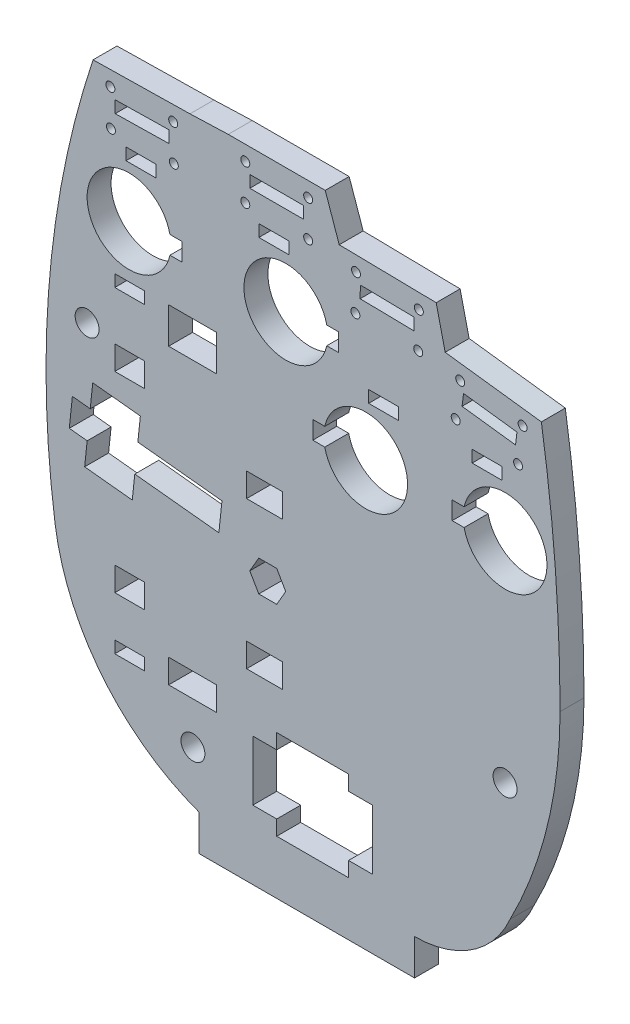
SolidWorks part; units mm, degrees
ref_plane "Front Plane" through (0, 0, 0) normal (0, 0, 1) x (1, 0, 0)
ref_plane "Top Plane" through (0, 0, 0) normal (0, 1, 0) x (1, 0, 0)
ref_plane "Right Plane" through (0, 0, 0) normal (1, 0, 0) x (0, 0, -1)
sketch "Sketch1" plane through (0, 0, 0) normal (0, 0, 1) x (1, 0, 0)
  line L0 (-4.5, 78.51) -> (-4.5, 76.51)
  line L1 (4.5, 78.51) -> (-4.5, 78.51)
  line L2 (-12.9786, -18) -> (-12.9786, -24)
  line L3 (-9.666, 24.0723) -> (-9.153, 28.9531)
  line L4 (-4.5, 76.51) -> (4.5, 76.51)
  line L5 (4.5, 76.51) -> (4.5, 78.51)
  line L6 (-34.6568, 26.6989) -> (-34.1438, 31.5798)
  line L7 (10.3588, 63.1512) -> (10.3588, 60.1512)
  line L8 (-8.1, 82.51) -> (8.1, 82.51)
  line L9 (8.3588, 63.1512) -> (10.3588, 63.1512)
  line L10 (10.4412, 75.8064) -> (26.6388, 75.5236)
  line L11 (32.6473, 57.3216) -> (37.6473, 57.3216)
  line L12 (0, 0) -> (-22.59, 0) construction
  line L13 (10.3588, 60.1512) -> (8.3588, 60.1512)
  line L14 (-17.8416, 63.1512) -> (-15.8416, 63.1512)
  line L15 (-15.8416, 63.1512) -> (-15.8416, 60.1512)
  line L16 (-15.8416, 60.1512) -> (-17.8416, 60.1512)
  line L17 (32.6473, 55.3216) -> (37.6473, 55.3216)
  line L18 (37.6473, 55.3216) -> (37.6473, 57.3216)
  line L19 (32.6473, 57.3216) -> (32.6473, 55.3216)
  line L20 (-27.0195, 78.062) -> (-18.0208, 78.2192)
  line L21 (-27.0195, 78.062) -> (-26.9845, 76.0623)
  line L22 (-10.0543, 52.8756) -> (-18.0543, 52.8756)
  line L23 (-9.153, 28.9531) -> (-23.2041, 30.43)
  line L24 (-26.9845, 76.0623) -> (-17.9858, 76.2195)
  line L25 (-24.1352, 21.571) -> (-32.0914, 22.4072)
  line L26 (-32.0914, 22.4072) -> (-31.6733, 26.3853)
  line L27 (-23.7171, 25.5491) -> (-9.666, 24.0723)
  line L28 (-17.9858, 76.2195) -> (-18.0208, 78.2192)
  line L29 (15.3631, 57.3216) -> (20.3631, 57.3216)
  line L30 (15.3631, 55.3216) -> (20.3631, 55.3216)
  line L31 (-12.9786, -24) -> (23.0214, -24)
  line L32 (20.3631, 55.3216) -> (20.3631, 57.3216)
  line L33 (23.0214, -24) -> (23.0214, -18)
  line L34 (15.3631, 57.3216) -> (15.3631, 55.3216)
  line L35 (-2.9786, 72.1512) -> (2.0214, 72.1512)
  line L36 (13.9709, 71.7441) -> (13.936, 69.7444)
  line L37 (13.936, 69.7444) -> (22.9346, 69.5874)
  line L38 (8.0257, 48.3216) -> (6.0257, 48.3216)
  line L39 (-2.9786, 70.1512) -> (2.0214, 70.1512)
  line L40 (22.9695, 71.5871) -> (13.9709, 71.7441)
  line L41 (6.0257, 48.3216) -> (6.0257, 45.3216)
  line L42 (22.9346, 69.5874) -> (22.9695, 71.5871)
  line L43 (-22.59, 0) -> (-22.59, 82.14) construction
  line L44 (2.0214, 70.1512) -> (2.0214, 72.1512)
  line L45 (18.54, 75.665) -> (18.5934, 78.7251) construction
  line L46 (-2.9786, 72.1512) -> (-2.9786, 70.1512)
  line L47 (40.1436, 63.5476) -> (31.2139, 64.6755)
  line L48 (6.0257, 45.3216) -> (8.0257, 45.3216)
  line L49 (29.3099, 45.3216) -> (31.3099, 45.3216)
  line L50 (29.3099, 48.3216) -> (29.3099, 45.3216)
  line L51 (31.3099, 48.3216) -> (29.3099, 48.3216)
  line L52 (-22.786, 34.408) -> (-30.7422, 35.2443)
  line L53 (31.2139, 64.6755) -> (30.9632, 62.6912)
  line L54 (-25.179, 72.1512) -> (-20.179, 72.1512)
  line L55 (-30.6888, 81.9985) -> (-14.4912, 82.2815)
  line L56 (44.2162, 67.065) -> (28.1438, 69.095)
  line L57 (-25.179, 70.1512) -> (-20.179, 70.1512)
  line L58 (30.9632, 62.6912) -> (39.893, 61.5633)
  line L59 (-20.179, 70.1512) -> (-20.179, 72.1512)
  line L60 (-25.179, 72.1512) -> (-25.179, 70.1512)
  line L61 (39.893, 61.5633) -> (40.1436, 63.5476)
  line L62 (-34.6568, 26.6989) -> (-31.6733, 26.3853)
  line L63 (-4, -2.5) -> (0, -2.5)
  line L64 (12, 0) -> (0, 0)
  line L65 (12, 0) -> (12, -2.5)
  line L66 (12, -15) -> (0, -15)
  line L67 (-30.7422, 35.2443) -> (-31.1603, 31.2662)
  line L68 (-23.2041, 30.43) -> (-22.786, 34.408)
  line L69 (-34.1438, 31.5798) -> (-31.1603, 31.2662)
  line L70 (-24.1352, 21.571) -> (-23.7171, 25.5491)
  line L71 (16, -7.5) -> (38.9913, -7.5) construction
  line L72 (0, -15) -> (0, -12.5)
  line L73 (-4, -12.5) -> (-4, -2.5)
  line L74 (-4, -12.5) -> (0, -12.5)
  line L75 (0, -2.5) -> (0, 0)
  line L76 (0, 0) -> (0, 82.51) construction
  line L77 (-22.0543, 52.8756) -> (-27.0543, 52.8756)
  line L78 (-10.0543, -2.1244) -> (-18.0543, -2.1244)
  line L79 (-22.0543, -2.1244) -> (-27.0543, -2.1244)
  line L80 (0, 0) -> (18.54, 0) construction
  line L81 (16, -12.5) -> (12, -12.5)
  line L82 (16, -12.5) -> (16, -2.5)
  line L83 (16, -2.5) -> (12, -2.5)
  line L84 (12, -12.5) -> (12, -15)
  line L85 (-9.4095, 26.5127) -> (6.8402, 24.8048) construction
  line L86 (0, 23.7547) -> (-3, 23.7547)
  line L87 (-3, 23.7547) -> (-4.5, 21.1566)
  line L88 (-4.5, 21.1566) -> (-3, 18.5585)
  line L89 (18.54, 0) -> (18.54, 75.665) construction
  line L90 (0, 0) -> (36.18, 0) construction
  line L91 (36.18, 0) -> (36.18, 68.08) construction
  line L92 (28.1438, 69.095) -> (26.6388, 75.5236)
  line L93 (10.4412, 75.8064) -> (8.1, 82.51)
  line L94 (-8.1, 82.51) -> (-14.4912, 82.2815)
  line L95 (-34.6568, 26.6989) -> (47.3354, 26.6989) construction
  line L96 (35.6788, 64.1115) -> (36.18, 68.08) construction
  line L97 (-3, 18.5585) -> (0, 18.5585)
  line L98 (0, 18.5585) -> (1.5, 21.1566)
  line L99 (1.5, 21.1566) -> (0, 23.7547)
  line L100 (0, 18.5585) -> (-3, 23.7547) construction
  line L101 (0, 23.7547) -> (-3, 18.5585) construction
  line L102 (38.1473, 11.8216) -> (-37.0527, 11.8216) construction
  line L103 (-27.7956, 79.5486) -> (-30.6451, 79.4989) construction
  line L104 (0.9634, 10.717) -> (0.9634, 6.717)
  line L105 (0.9634, 6.717) -> (-5.0366, 6.717)
  line L106 (-5.0366, 6.717) -> (-5.0366, 10.717)
  line L107 (-5.0366, 10.717) -> (0.9634, 10.717)
  line L108 (-5.0366, 31.3356) -> (0.9634, 31.3356)
  line L109 (-5.0366, 35.3356) -> (-5.0366, 31.3356)
  line L110 (0.9634, 35.3356) -> (-5.0366, 35.3356)
  line L111 (0.9634, 31.3356) -> (0.9634, 35.3356)
  line L112 (-30.6451, 79.4989) -> (-30.6888, 81.9985) construction
  line L113 (-17.2971, 79.732) -> (-14.4475, 79.7819) construction
  line L114 (-14.4475, 79.7819) -> (-14.4912, 82.2815) construction
  line L115 (-22.5201, 78.1406) -> (-22.59, 82.14) construction
  line L116 (5.25, 80.01) -> (8.1, 80.01) construction
  line L117 (8.1, 80.01) -> (8.1, 82.51) construction
  line L118 (-5.25, 80.01) -> (-8.1, 80.01) construction
  line L119 (-22.0543, -0.1244) -> (-27.0543, -0.1244)
  line L120 (-8.1, 80.01) -> (-8.1, 82.51) construction
  line L121 (-10.0543, 1.8756) -> (-10.0543, -2.1244)
  line L122 (30.6581, 66.2576) -> (27.8306, 66.6147) construction
  line L123 (-10.0543, 52.8756) -> (-10.0543, 46.8756)
  line L124 (-10.0543, 1.8756) -> (-18.0543, 1.8756)
  line L125 (-18.0543, 1.8756) -> (-18.0543, -2.1244)
  line L126 (27.8306, 66.6147) -> (28.1438, 69.095) construction
  line L127 (13.2472, 73.257) -> (10.3976, 73.3067) construction
  line L128 (-22.0543, -0.1244) -> (-22.0543, -2.1244)
  line L129 (-27.0543, -0.1244) -> (-27.0543, -2.1244)
  line L130 (30.6581, 66.2576) -> (29.9062, 60.3049) construction
  line L131 (-10.0543, 46.8756) -> (-18.0543, 46.8756)
  line L132 (-27.0543, 52.8756) -> (-27.0543, 50.8756)
  line L133 (-18.0543, 46.8756) -> (-18.0543, 52.8756)
  line L134 (10.4412, 75.8064) -> (10.3976, 73.3067) construction
  line L135 (-22.0543, 6.717) -> (-22.0543, 10.717)
  line L136 (-22.0543, 10.717) -> (-27.0543, 10.717)
  line L137 (-27.0543, 50.8756) -> (-22.0543, 50.8756)
  line L138 (-22.0543, 52.8756) -> (-22.0543, 50.8756)
  line L139 (-27.0543, 10.717) -> (-27.0543, 6.717)
  line L140 (-27.0543, 6.717) -> (-22.0543, 6.717)
  line L141 (-27.0543, 38.7272) -> (-22.0543, 38.7272)
  line L142 (-22.0543, 38.7272) -> (-22.0543, 42.7272)
  line L143 (-22.0543, 42.7272) -> (-27.0543, 42.7272)
  line L144 (-27.0543, 42.7272) -> (-27.0543, 38.7272)
  line L145 (23.7456, 73.0738) -> (26.5951, 73.024) construction
  line L146 (26.5951, 73.024) -> (26.6388, 75.5236) construction
  line L147 (41.0753, 64.9418) -> (43.9029, 64.5847) construction
  line L148 (41.0753, 64.9418) -> (40.3235, 58.9891) construction
  line L149 (40.3235, 58.9891) -> (43.151, 58.632) construction
  line L150 (43.151, 58.632) -> (43.9029, 64.5847) construction
  line L151 (23.7456, 73.0738) -> (23.6409, 67.0747) construction
  line L152 (13.2472, 73.257) -> (13.1425, 67.2579) construction
  line L153 (-17.2971, 79.732) -> (-17.1923, 73.733) construction
  line L154 (-27.7956, 79.5486) -> (-27.6908, 73.5496) construction
  line L155 (38.1473, 46.8216) -> (38.1473, 11.8216) construction
  arc A0 (-37.0527, 11.8216) -> (-30.6888, 81.9985) centre (116.3395, 33.2885) cw
  circle A1 centre (-1.5, 21.1566) radius 4.5 construction
  arc A2 (8.3588, 63.1512) -> (8.3588, 60.1512) centre (1.5214, 61.6512) ccw
  arc A3 (8.0257, 45.3216) -> (8.0257, 48.3216) centre (14.8631, 46.8216) ccw
  arc A4 (-17.8416, 63.1512) -> (-17.8416, 60.1512) centre (-24.679, 61.6512) ccw
  arc A5 (31.3099, 45.3216) -> (31.3099, 48.3216) centre (38.1473, 46.8216) ccw
  arc A6 (23.0214, -18) -> (38.9913, -7.5) centre (23.0214, -0.6053) ccw
  arc A7 (47.3354, 26.6989) -> (38.9913, -7.5) centre (-26.9196, 26.6989) cw
  arc A8 (-37.0527, 11.8216) -> (-12.9786, -18) centre (-0.147, 16.9865) ccw
  arc A9 (47.3354, 26.6989) -> (44.2162, 67.065) centre (-215.4084, 26.6989) ccw
  circle A11 centre (38.1473, 11.8216) radius 2
  circle A12 centre (-14, -9.1244) radius 2
  circle A18 centre (-5.25, 80.01) radius 0.75
  circle A22 centre (-31.6815, 43.4564) radius 2
  circle A49 centre (5.25, 80.01) radius 0.75
  circle A50 centre (5.25, 74.01) radius 0.75
  circle A51 centre (-5.25, 74.01) radius 0.75
  circle A52 centre (-27.7956, 79.5486) radius 0.75
  circle A53 centre (-17.2971, 79.732) radius 0.75
  circle A54 centre (-27.6908, 73.5496) radius 0.75
  circle A55 centre (-17.1923, 73.733) radius 0.75
  circle A56 centre (23.6409, 67.0747) radius 0.75
  circle A57 centre (13.1425, 67.2579) radius 0.75
  circle A58 centre (23.7456, 73.0738) radius 0.75
  circle A59 centre (13.2472, 73.257) radius 0.75
  circle A60 centre (29.9062, 60.3049) radius 0.7496
  circle A61 centre (41.0753, 64.9418) radius 0.7496
  circle A62 centre (30.6581, 66.2576) radius 0.7496
  circle A63 centre (40.3235, 58.9891) radius 0.7496
  dimension "D1" = 4
  dimension "D2" = 1.5
  dimension "D11" = 1.5214
  dimension "D12" = 2.0214
  dimension "D16" = 6.0257
  dimension "D17" = 4
  dimension "D18" = 8.3588
  dimension "D19" = 22.59
  dimension "D22" = 4
  dimension "D23" = 18.54
  dimension "D24" = 75.665
  dimension "D25" = 12
  dimension "D35" = 4
  dimension "D36" = 16.2
  dimension "D37" = 2
  dimension "D38" = 29.3099
  dimension "D39" = 2.85
  dimension "D40" = 46.8216
  dimension "D43" = 2.85
  dimension "D44" = 24.679
  dimension "D45" = 9
  dimension "D46" = 0.7292
  dimension "D47" = 4.9078
  dimension "D49" = 5.0366
  dimension "D51" = 9.666
  dimension "D55" = 24
  dimension "D56" = 15.8416
  dimension "D13" = 4
  dimension "D58" = 2.5
  dimension "D59" = 18.0543
  dimension "D60" = 8.1
  dimension "D61" = 6
  dimension "D63" = 22.0543
  dimension "D64" = 2.5
  dimension "D65" = 2.85
  dimension "D52" = 10.0543
  dimension "D48" = 25.1285
  dimension "D53" = 12.9786
  dimension "D57" = 4
  dimension "D69" = 6
  dimension "D70" = 2.5
  dimension "D71" = 1.8756
  dimension "D79" = 43.4564
  dimension "D82" = 55.3216
  dimension "D67" = 2.5
  dimension "D68" = 31.6815
  dimension "D5" = 7
  dimension "D29" = 2.5
  dimension "D83" = 8.1
  dimension "D85" = 2
  dimension "D10" = 0.9634
  dimension "D14" = 82.51
  dimension "D15" = 3
  dimension "D20" = 10
  dimension "D21" = 82.14
  dimension "D26" = 15.3631
  dimension "D27" = 2.5
  dimension "D28" = 0
  dimension "D30" = 20.3631
  dimension "D31" = 36.18
  dimension "D32" = 68.08
  dimension "D33" = 23.0214
  dimension "D34" = 6
  dimension "D41" = 14.8631
  dimension "D42" = 32.6473
  dimension "D50" = 9.153
  dimension "D54" = 14
  dimension "D62" = 20.179
  dimension "D66" = 2.85
  dimension "D72" = 6.717
  dimension "D73" = 9.0001
  dimension "D74" = 9.0007
  dimension "D75" = 35
  dimension "D76" = 21.571
  dimension "D77" = 31.3356
  dimension "D78" = 6
  dimension "D80" = 45.3216
  dimension "D81" = 46.8756
  dimension "D84" = 60.1512
  dimension "D86" = 70.1512
  dimension "D93" = 9.1244
extrude "Boss-Extrude1" add sketch "Sketch1" along normal blind 4
equation "\"D14@Sketch1\"= \"HL@parametersSketch@prostheticParameters.SLDPRT\" * 0.446'Mioddle Base Frame "
equation "\"D19@Sketch1\"= \"HB@parametersSketch@prostheticParameters.SLDPRT\" * 0.251'Index Base Frame X"
equation "\"D21@Sketch1\"= \"HL@parametersSketch@prostheticParameters.SLDPRT\" * 0.444'Index Base Frame Y"
equation "\"D23@Sketch1\"= \"HB@parametersSketch@prostheticParameters.SLDPRT\" * 0.206'Ring Base Frame X"
equation "\"D24@Sketch1\"= \"HL@parametersSketch@prostheticParameters.SLDPRT\" * 0.409'Ring Base Frame Y"
equation "\"D31@Sketch1\"= \"HB@parametersSketch@prostheticParameters.SLDPRT\" * 0.402'Pinky Base Frame X"
equation "\"D32@Sketch1\"= \"HL@parametersSketch@prostheticParameters.SLDPRT\" * 0.368'Pinky Base Frame Y"
equation "\"D36@Sketch1\"= \"fingerWidth@parametersSketch@prostheticParameters.SLDPRT\"'Fingers Width"
equation "\"D76@Sketch1\"= \"HL@parametersSketch@prostheticParameters.SLDPRT\" * 0.1166'Hole Thumb Y"
equation "\"D51@Sketch1\"= \"HB@parametersSketch@prostheticParameters.SLDPRT\" * 0.1074'Hole Thumb X1"
equation "\"D50@Sketch1\" = \"HB@parametersSketch@prostheticParameters.SLDPRT\" * 0.1017'Hole Thumb X2"
equation "\"D73@Sketch1\"= \"fingerWidth@parametersSketch@prostheticParameters.SLDPRT\" * 0.55556"
equation "\"D74@Sketch1\"= \"fingerWidth@parametersSketch@prostheticParameters.SLDPRT\" * 0.5556"
equation "\"D60@Sketch1\"= \"fingerWidth@parametersSketch@prostheticParameters.SLDPRT\" / 2"
equation "\"D83@Sketch1\"= \"fingerWidth@parametersSketch@prostheticParameters.SLDPRT\" / 2"
